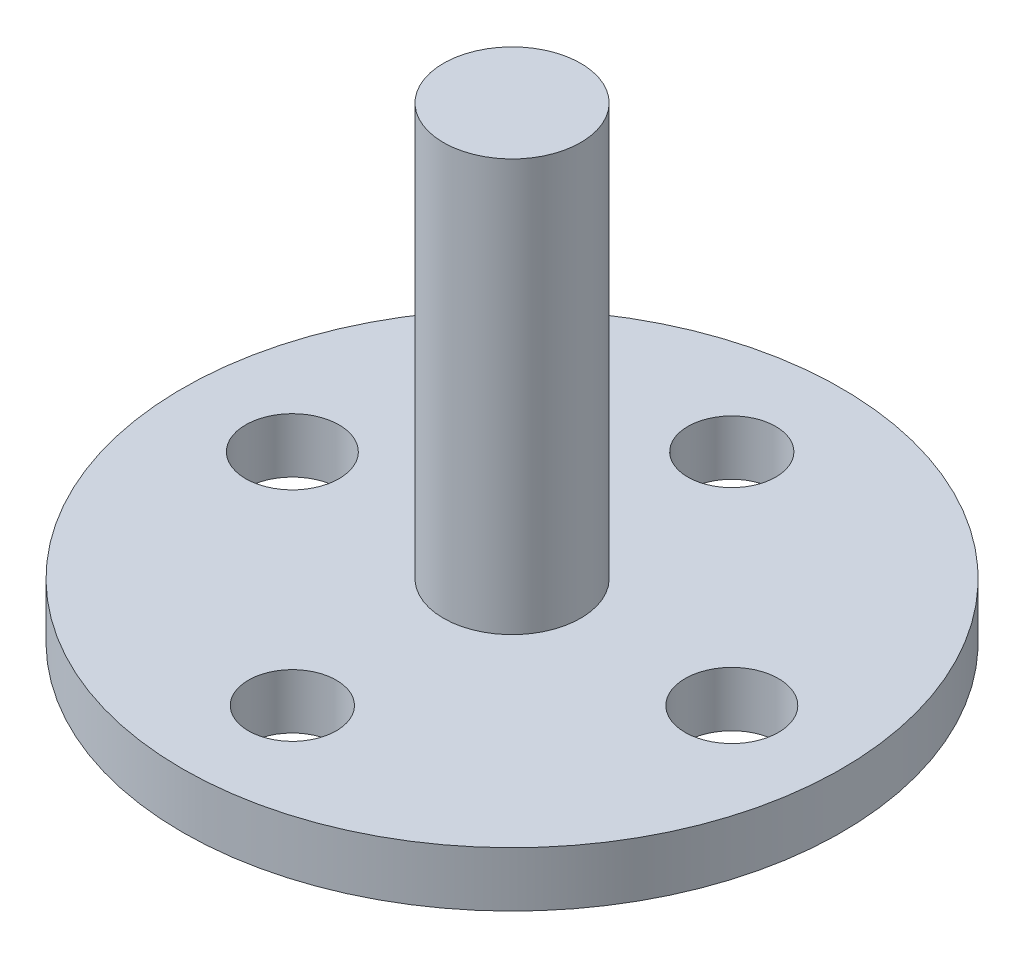
SolidWorks part; units mm, degrees
ref_plane "前视基准面" through (0, 0, 0) normal (0, 0, 1) x (1, 0, 0)
ref_plane "上视基准面" through (0, 0, 0) normal (0, 1, 0) x (1, 0, 0)
ref_plane "右视基准面" through (0, 0, 0) normal (1, 0, 0) x (0, 0, -1)
sketch "草图1" plane through (0, 0, 0) normal (0, 1, 0) x (1, 0, 0)
  circle A0 centre (0, 0) radius 12
  circle A1 centre (-8, 0) radius 1.7
  circle A2 centre (0, 8) radius 1.6
  circle A3 centre (8, 0) radius 1.7
  circle A4 centre (0, -8) radius 1.6
  dimension "D1" = 24
  dimension "D2" = 8
  dimension "D3" = 8
  dimension "D4" = 8
  dimension "D5" = 8
  dimension "D6" = 3.2
  dimension "D7" = 3.4
  dimension "D8" = 3.2
  dimension "D9" = 3.4
extrude "凸台-拉伸1" add sketch "草图1" along normal blind 2
sketch "草图2" plane through (0, 2, 0) normal (0, 1, 0) x (1, 0, 0)
  circle A0 centre (0, 0) radius 2.5
  dimension "D1" = 5
extrude "凸台-拉伸2" add sketch "草图2" along normal blind 15
